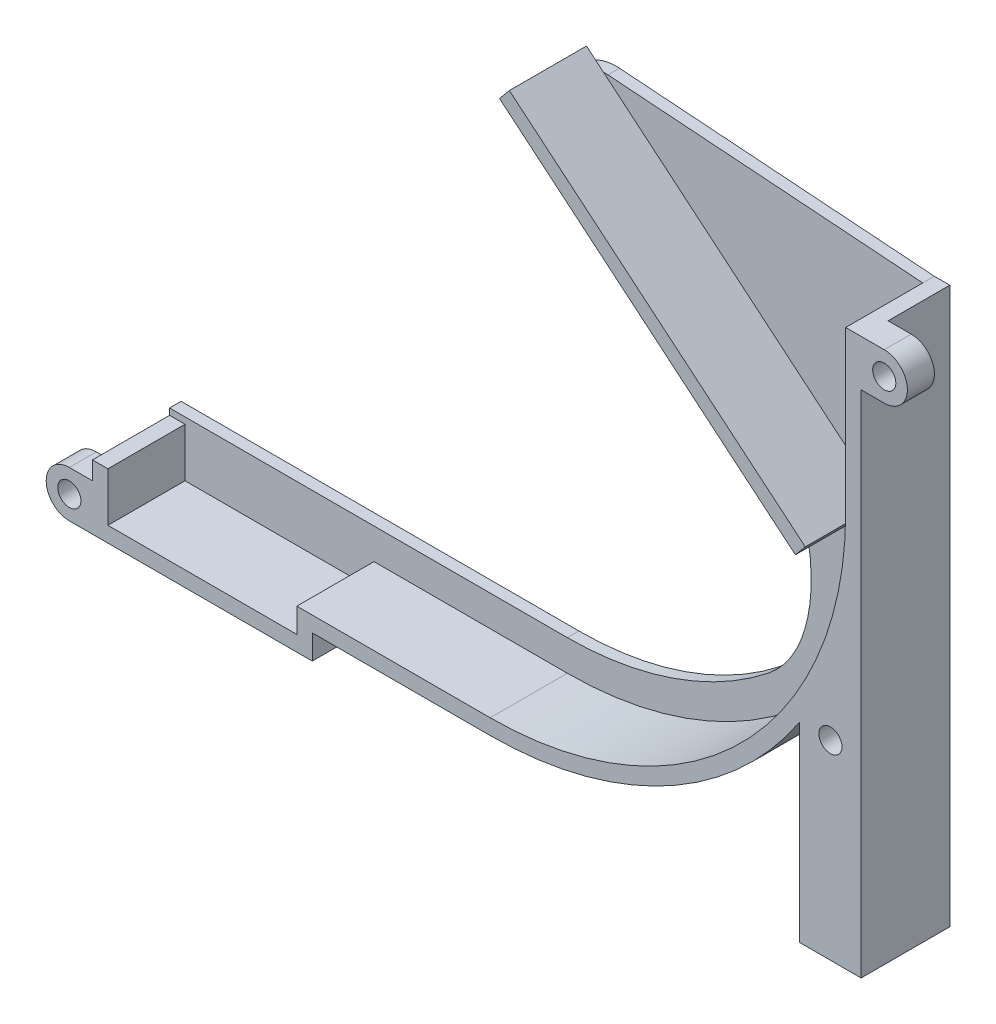
SolidWorks part; units mm, degrees
ref_plane "Front Plane" through (0, 0, 0) normal (0, 0, 1) x (1, 0, 0)
ref_plane "Top Plane" through (0, 0, 0) normal (0, 1, 0) x (1, 0, 0)
ref_plane "Right Plane" through (0, 0, 0) normal (1, 0, 0) x (0, 0, -1)
sketch "Sketch1" plane through (0, 0, 0) normal (0, 0, 1) x (1, 0, 0)
  line L0 (-18.1262, 8.4524) -> (18.1262, -8.4524) construction
  line L1 (0, 0) -> (25.201, 0) construction
  line L2 (23.1262, 11.4863) -> (23.1262, -9.2963)
  line L3 (-22.9677, -55.3901) -> (-48.0407, -55.3901)
  line L4 (-48.0407, -55.3901) -> (-48.0407, -58.5651)
  line L5 (-48.0407, -58.5651) -> (-72.5407, -58.5651)
  line L6 (-72.5407, -58.5651) -> (-72.5407, -52.2151)
  line L7 (25.1262, 11.4863) -> (25.1262, -9.2963)
  line L8 (-22.9677, -57.3901) -> (-46.0407, -57.3901)
  line L9 (-46.0407, -57.3901) -> (-46.0407, -60.5651)
  line L10 (-46.0407, -60.5651) -> (-74.5407, -60.5651)
  line L11 (-74.5407, -60.5651) -> (-74.5407, -52.2151)
  line L12 (-72.5407, -52.2151) -> (-74.5407, -52.2151)
  line L13 (23.1262, 11.4863) -> (25.1262, 11.4863)
  arc A0 (23.1262, -9.2963) -> (-22.9677, -55.3901) centre (-22.9677, -9.2963) cw
  arc A1 (25.1262, -9.2963) -> (-22.9677, -57.3901) centre (-22.9677, -9.2963) cw
  point P3 (0, 0)
  dimension "D1" = 40
  dimension "D2" = 25
  dimension "D3" = 5
  dimension "D4" = 24.5
  dimension "D5" = 3.175
  dimension "D6" = 6.35
  dimension "D7" = 2
extrude "Boss-Extrude1" add sketch "Sketch1" along normal blind 10
sketch "Sketch2" plane through (0, 0, 0) normal (0, 0, -1) x (-1, 0, 0)
  line L1 (-23.1262, 11.4863) -> (17.6936, 14.4368)
  line L4 (18.1262, 8.4524) -> (-18.1262, -8.4524) construction
  line L5 (-7.5168, -3.5051) -> (5.2321, 2.4397) construction
  line L6 (-8.1507, -2.1457) -> (4.5981, 3.7992) construction
  line L7 (-6.8829, -4.8646) -> (5.866, 1.0803) construction
  line L11 (52.0407, -51.3901) -> (74.5407, -51.3901)
  line L38 (74.5407, -51.3901) -> (74.5407, -52.2151)
  line L39 (-25.1262, 11.4863) -> (-23.1262, 11.4863)
  line L48 (-19.1262, -9.2963) -> (-19.1262, 15.4863)
  line L49 (-19.1262, 15.4863) -> (-29.1262, 15.4863)
  line L50 (-29.1262, 15.4863) -> (-29.1262, -9.2963)
  line L51 (22.9677, -61.3901) -> (42.0407, -61.3901)
  line L52 (42.0407, -61.3901) -> (42.0407, -64.5651)
  line L53 (42.0407, -64.5651) -> (78.5407, -64.5651)
  line L54 (78.5407, -64.5651) -> (78.5407, -48.2151)
  line L55 (78.5407, -48.2151) -> (68.5407, -48.2151)
  line L56 (68.5407, -48.2151) -> (68.5407, -54.5651)
  line L57 (68.5407, -54.5651) -> (52.0407, -54.5651)
  line L58 (52.0407, -54.5651) -> (52.0407, -51.3901)
  line L59 (52.0407, -51.3901) -> (22.9677, -51.3901)
  line L71 (52.0407, -51.3901) -> (22.9677, -51.3901)
  line L74 (-23.1262, 11.4863) -> (-25.1262, 11.4863)
  line L75 (-25.1262, 11.4863) -> (-25.1262, -9.2963)
  line L76 (22.9677, -57.3901) -> (46.0407, -57.3901)
  line L77 (46.0407, -57.3901) -> (46.0407, -60.5651)
  line L78 (46.0407, -60.5651) -> (74.5407, -60.5651)
  line L79 (74.5407, -60.5651) -> (74.5407, -52.2151)
  line L80 (74.5407, -52.2151) -> (72.5407, -52.2151)
  line L81 (72.5407, -52.2151) -> (72.5407, -58.5651)
  line L82 (72.5407, -58.5651) -> (48.0407, -58.5651)
  line L83 (48.0407, -58.5651) -> (48.0407, -55.3901)
  line L84 (48.0407, -55.3901) -> (22.9677, -55.3901)
  line L85 (-23.1262, -9.2963) -> (-23.1262, 11.4863)
  line L87 (-25.1262, 11.4863) -> (-25.1262, -9.2963)
  line L88 (22.9677, -57.3901) -> (46.0407, -57.3901)
  line L89 (46.0407, -57.3901) -> (46.0407, -60.5651)
  line L90 (46.0407, -60.5651) -> (74.5407, -60.5651)
  line L91 (74.5407, -60.5651) -> (74.5407, -52.2151)
  arc A1 (20.6619, 3.0145) -> (17.6936, 14.4368) centre (18.1262, 8.4524) ccw
  arc A6 (-8.1507, -2.1457) -> (-6.8829, -4.8646) centre (-7.5168, -3.5051) ccw construction
  arc A7 (5.866, 1.0803) -> (4.5981, 3.7992) centre (5.2321, 2.4397) ccw construction
  arc A8 (-29.1262, -9.2963) -> (22.9677, -61.3901) centre (22.9677, -9.2963) ccw
  arc A9 (-19.1262, -9.2963) -> (22.9677, -51.3901) centre (22.9677, -9.2963) ccw
  arc A11 (-3.1097, -42.3396) -> (22.9677, -51.3901) centre (22.9677, -9.2963) ccw
  arc A12 (-25.1262, -9.2963) -> (22.9677, -57.3901) centre (22.9677, -9.2963) ccw
  arc A13 (-23.1262, -9.2963) -> (22.9677, -55.3901) centre (22.9677, -9.2963) ccw
  arc A14 (-25.1262, -9.2963) -> (22.9677, -57.3901) centre (22.9677, -9.2963) ccw
  spline S0 degree 3 poles (20.6619, 3.0145) (14.467, 0.1258) (-11.1415, -11.2332) (-9.493, -37.302) (-3.1097, -42.3396) knots 0 0 0 0 0.582936 1 1 1 1
  point P20 (-1.1424, -0.5327)
  dimension "D3" = 1.5
  dimension "D4" = 6
  dimension "D1" = 4
  dimension "D2" = 0
extrude "Boss-Extrude2" add sketch "Sketch2" along normal blind 1.5
sketch "Sketch6" plane through (0, 0, 0) normal (0, 0, 1) x (1, 0, 0)
  line L0 (-21.7653, 14.7535) -> (16.6051, -17.3044)
  line L1 (16.6051, -17.3044) -> (17.8874, -15.7696)
  line L2 (17.8874, -15.7696) -> (-20.483, 16.2883)
  line L3 (-20.483, 16.2883) -> (-21.7653, 14.7535)
  line L4 (-21.7653, 14.7535) -> (17.8874, -15.7696) construction
  line L5 (-20.483, 16.2883) -> (16.6051, -17.3044) construction
  point P4 (16.485, -15.4603)
  point P5 (-20.5928, 15.535)
  dimension "D1" = 2
  dimension "D2" = 50
extrude "Boss-Extrude4" add sketch "Sketch6" along normal up to surface (10 mm away) up to face at (-29.4464, -41.6699, 10)
sketch "Sketch4" plane through (0, 0, -1.5) normal (0, 0, -1) x (-1, 0, 0)
  line L0 (-25.1262, -9.2963) -> (-25.1262, -60.5651)
  line L1 (-25.1262, -60.5651) -> (-17.1262, -60.5651)
  line L2 (-17.1262, -60.5651) -> (-17.1262, -35.8576)
  line L3 (46.0407, -60.5651) -> (74.5407, -60.5651) construction
  line L4 (-28.1262, 11.4863) -> (-25.1262, 11.4863)
  line L5 (-28.1262, 5.4863) -> (-25.1262, 5.4863)
  line L6 (-25.1262, 11.4863) -> (-25.1262, -9.2963) construction
  line L7 (-25.1262, 11.4863) -> (-25.1262, 5.4863)
  line L8 (74.5407, -60.5651) -> (74.5407, -51.3901) construction
  line L9 (74.5407, -60.5651) -> (74.5407, -54.5651)
  line L10 (74.5407, -60.5651) -> (77.5407, -60.5651)
  line L11 (77.5407, -54.5651) -> (74.5407, -54.5651)
  arc A0 (-25.1262, -9.2963) -> (22.9677, -57.3901) centre (22.9677, -9.2963) ccw construction
  arc A3 (-28.1262, 11.4863) -> (-28.1262, 5.4863) centre (-28.1262, 8.4863) ccw
  arc A4 (77.5407, -60.5651) -> (77.5407, -54.5651) centre (77.5407, -57.5651) ccw
  arc A5 (-25.1262, -9.2963) -> (22.9677, -57.3901) centre (22.9677, -9.2963) ccw construction
  arc A6 (-25.1262, -9.2963) -> (-17.1262, -35.8576) centre (22.9677, -9.2963) ccw
  circle A7 centre (-28.1262, 8.4863) radius 1.5
  circle A8 centre (77.5407, -57.5651) radius 1.5
  circle A9 centre (-21.1479, -35.8576) radius 1.5
  dimension "D2" = 3
  dimension "D3" = 6
  dimension "D4" = 3
  dimension "D5" = 3
  dimension "D1" = 8
extrude "Boss-Extrude3" add sketch "Sketch4" against normal up to surface (11.5 mm away) up to face at (-29.4464, -41.6699, 10)
sketch "Sketch5" plane through (0, 0, -1.5) normal (0, 0, -1) x (-1, 0, 0)
  line L0 (-25.1262, 5.4863) -> (-25.1262, 11.4863)
  line L1 (74.5407, -54.5651) -> (74.5407, -60.5651)
  line L12 (-23.1262, 11.4863) -> (-28.1262, 11.4863)
  line L13 (-28.1262, 5.4863) -> (-25.1262, 5.4863)
  line L14 (-25.1262, 5.4863) -> (-25.1262, -60.5651)
  line L15 (-25.1262, -60.5651) -> (-17.1262, -60.5651)
  line L16 (-17.1262, -60.5651) -> (-17.1262, -35.8576)
  line L17 (22.9677, -57.3901) -> (46.0407, -57.3901)
  line L18 (46.0407, -57.3901) -> (46.0407, -60.5651)
  line L19 (46.0407, -60.5651) -> (77.5407, -60.5651)
  line L20 (77.5407, -54.5651) -> (74.5407, -54.5651)
  line L21 (74.5407, -54.5651) -> (74.5407, -51.3901)
  line L22 (74.5407, -51.3901) -> (22.9677, -51.3901)
  line L23 (17.6936, 14.4368) -> (-23.1262, 11.4863)
  line L24 (-25.1262, 11.4863) -> (-28.1262, 11.4863)
  line L25 (-28.1262, 5.4863) -> (-25.1262, 5.4863)
  line L31 (74.5407, -60.5651) -> (77.5407, -60.5651)
  line L32 (77.5407, -54.5651) -> (74.5407, -54.5651)
  arc A1 (77.5407, -60.5651) -> (77.5407, -54.5651) centre (77.5407, -57.5651) ccw
  arc A2 (77.5407, -60.5651) -> (77.5407, -54.5651) centre (77.5407, -57.5651) ccw construction
  circle A3 centre (-21.1479, -35.8576) radius 3
  arc A9 (-28.1262, 11.4863) -> (-28.1262, 5.4863) centre (-28.1262, 8.4863) ccw
  arc A10 (-17.1262, -35.8576) -> (22.9677, -57.3901) centre (22.9677, -9.2963) ccw
  arc A11 (77.5407, -60.5651) -> (77.5407, -54.5651) centre (77.5407, -57.5651) ccw
  arc A12 (-3.1097, -42.3396) -> (22.9677, -51.3901) centre (22.9677, -9.2963) ccw
  arc A13 (20.6619, 3.0145) -> (17.6936, 14.4368) centre (18.1262, 8.4524) ccw
  arc A14 (-28.1262, 11.4863) -> (-28.1262, 5.4863) centre (-28.1262, 8.4863) ccw
  arc A16 (77.5407, -60.5651) -> (77.5407, -54.5651) centre (77.5407, -57.5651) ccw
  spline S1 degree 3 poles (457.0873, 845.4694) (81.3885, -175.3064) (-156.9601, 73.8373) (229.1068, -13.9969) (-977.9948, -48.7502) knots -1.766509 -1.766509 -1.766509 -1.766509 0.417064 3.019761 3.019761 3.019761 3.019761 only from (-3.1097, -42.3396) to (20.6619, 3.0145)
  line M3 (-23.1262, 11.4863) -> (-28.1262, 11.4863)
  arc M4 (-28.1262, 11.4863) -> (-28.1262, 5.4863) centre (-28.1262, 8.4863) ccw
  line M5 (-28.1262, 5.4863) -> (-25.1262, 5.4863)
  line M12 (46.0407, -60.5651) -> (77.5407, -60.5651)
  arc M13 (77.5407, -60.5651) -> (77.5407, -54.5651) centre (77.5407, -57.5651) ccw
  line M14 (77.5407, -54.5651) -> (74.5407, -54.5651)
  circle M25 centre (-21.1479, -35.8576) radius 1.5
  circle M26 centre (-28.1262, 8.4863) radius 1.5
  circle M27 centre (77.5407, -57.5651) radius 1.5
  dimension "D1" = 6
  dimension "D2" = 0
extrude "Cut-Extrude1" cut sketch "Sketch5" against normal blind 8 contours L1 M14 M12 M13 M27 | A3 M25 | L0 M5 M3 M4 M26
